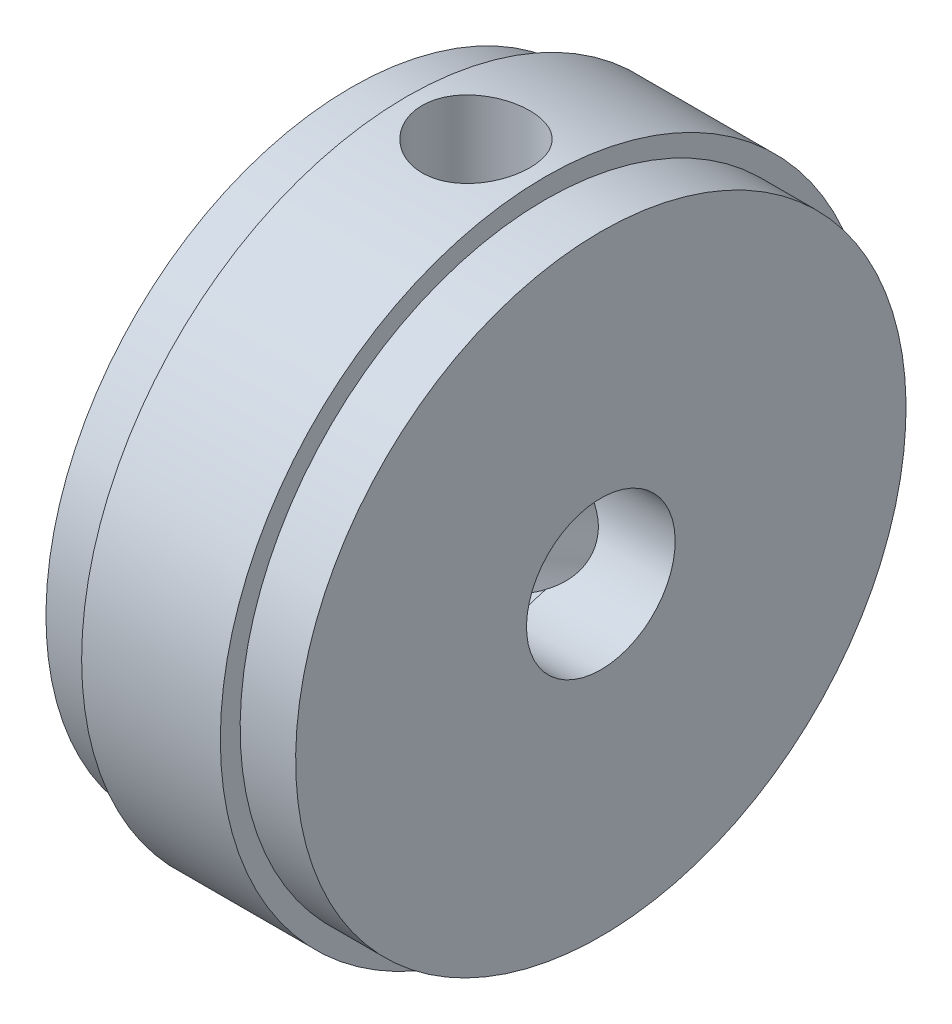
SolidWorks part; units mm, degrees
ref_plane "Front Plane" through (0, 0, 0) normal (0, 0, 1) x (1, 0, 0)
ref_plane "Top Plane" through (0, 0, 0) normal (0, 1, 0) x (1, 0, 0)
ref_plane "Right Plane" through (0, 0, 0) normal (1, 0, 0) x (0, 0, -1)
sketch "Sketch1" plane through (0, 0, 0) normal (0, 0, 1) x (1, 0, 0)
  line L0 (4, 0) -> (-4, 0)
  line L1 (-4, 0) -> (-4, 9.779)
  line L2 (-4, 9.779) -> (-2.222, 9.779)
  line L3 (-2.222, 9.779) -> (-2.222, 10.414)
  line L4 (-2.222, 10.414) -> (2.222, 10.414)
  line L5 (0, 6.9798) -> (0, -1.4779) construction
  line L6 (2.222, 9.779) -> (2.222, 10.414)
  line L7 (4, 9.779) -> (2.222, 9.779)
  line L8 (4, 0) -> (4, 9.779)
  line L9 (8.4308, 0) -> (-8.6385, 0) construction
  point P10 (0, 10.414)
  point P13 (0, 0)
  dimension "D1" = 4
  dimension "D2" = 1.778
  dimension "D3" = 9.779
  dimension "D4" = 0.635
revolve "Revolve1" add sketch "Sketch1" angle 360 about L9
sketch "Sketch2" plane through (-4, 0, 0) normal (-1, 0, 0) x (0, 0, 1)
  circle A0 centre (0, 0) radius 2.3813
  dimension "D1" = 4.7625
extrude "Cut-Extrude1" cut sketch "Sketch2" against normal through all
sketch "Sketch3" plane through (0, 0, 0) normal (1, 0, 0) x (0, 0, -1)
  line L0 (0, 0) -> (0, 10.414) construction
  circle A0 centre (0, 0) radius 10.414 construction
ref_plane "Plane1" through (0, 10.414, 0) normal (0, 1, 0) x (-1, 0, 0)
hole_wizard "#8-32 Tapped Hole1" positions "Sketch5" profile "Sketch4" tap size "#8-32" standard "Ansi Inch"
sketch "Sketch5" plane through (0, 10.414, 0) normal (0, 1, 0) x (-1, 0, 0)
  point P0 (0, 0)
sketch "Sketch4" plane through (0, 10.414, 0) normal (1, 0, 0) x (0, 0, 1)
  line L0 (0, 0) -> (0, 13.4838)
  line L1 (0, 13.4838) -> (1.7272, 12.446)
  line L2 (1.7272, 12.446) -> (1.7272, 0)
  line L5 (1.7272, 0) -> (0, 0)
  line L10 (0, 13.4838) -> (-1.7272, 12.446) construction
  line L11 (0, -6.35) -> (0, 107.95) construction
  dimension "Tap Drill Dia." = 3.4544
  dimension "Tap Drill Depth" = 12.446
  dimension "Drill Angle" = 118
sketch "Sketch9" plane through (4, 0, 0) normal (1, 0, 0) x (0, 0, -1)
  point P0 (0, 0)
pattern_circular "CirPattern1" count 2 over 120 about axis through (4, 0, 0) along (-1, 0, 0) of "#8-32 Tapped Hole1"
